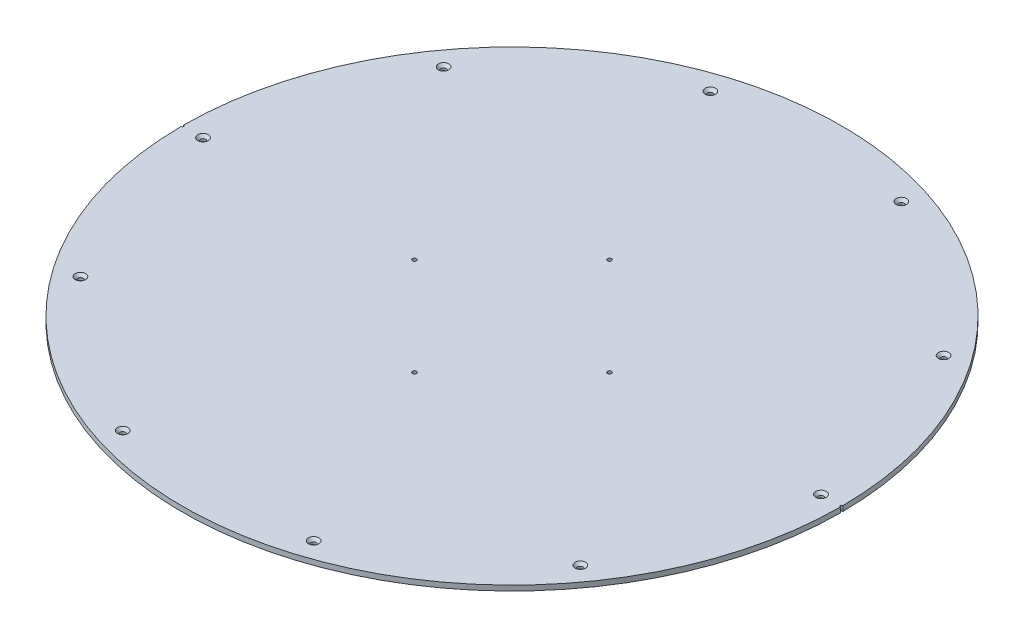
SolidWorks part; units mm, degrees
material "PC High Viscosity"
ref_plane "Front Plane" through (0, 0, 0) normal (0, 0, 1) x (1, 0, 0)
ref_plane "Top Plane" through (0, 0, 0) normal (0, 1, 0) x (1, 0, 0)
ref_plane "Right Plane" through (0, 0, 0) normal (1, 0, 0) x (0, 0, -1)
sketch "Sketch1" plane through (0, 0, 0) normal (0, 1, 0) x (1, 0, 0)
  circle A0 centre (0, 0) radius 406.4
  dimension "D1" = 812.8
extrude "Boss-Extrude1" add sketch "Sketch1" along normal blind 6.35
hole_wizard "7/8 (1.125) Diameter Hole1" positions "Sketch2" profile "Sketch3" hole size "7/8" standard "ANSI Inch"
sketch "Sketch2" plane through (0, 6.35, 0) normal (0, 1, 0) x (1, 0, 0)
  point P0 (0, 0)
sketch "Sketch3" plane through (0, 6.35, 0) normal (1, 0, 0) x (0, 0, 1)
  line L0 (0, 0) -> (0, 6.35)
  line L1 (0, 6.35) -> (14.2875, 6.35)
  line L2 (14.2875, 6.35) -> (14.2875, 0)
  line L5 (14.2875, 0) -> (0, 0)
  line L11 (0, -6.35) -> (0, 107.95) construction
  dimension "Thru Hole Dia." = 28.575
  dimension "Thru Hole Depth" = 6.35
hole_wizard "CSK for 1/4 Flat Head Machine Screw1" positions "Sketch4" profile "Sketch6" countersink size "1/4" standard "ANSI Inch"
sketch "Sketch4" plane through (0, 6.35, 0) normal (0, 1, 0) x (1, 0, 0)
  line L1 (0, 0) -> (-238.5946, -328.3973) construction
  line L2 (0, 0) -> (-386.0541, -125.4366) construction
  line L3 (0, 0) -> (-386.0541, 125.4366) construction
  line L4 (0, 0) -> (-238.5946, 328.3973) construction
  line L5 (0, 0) -> (0, 405.9213) construction
  line L6 (0, 0) -> (238.5946, 328.3973) construction
  line L7 (0, 0) -> (386.0541, 125.4366) construction
  line L8 (0, 0) -> (386.0541, -125.4366) construction
  line L9 (0, 0) -> (0, -406.4) construction
  line L11 (0, 0) -> (238.8759, -328.7845) construction
  circle A0 centre (0, 0) radius 406.4 construction
  circle A1 centre (0, 0) radius 76.2
  circle A2 centre (0, 0) radius 381
  point P86 (71.842, -71.842)
  point P88 (0, -101.6)
  point P90 (-71.842, -71.842)
  point P92 (-101.6, 0)
  point P94 (-71.842, 71.842)
  point P159 (117.7355, 362.3525)
  point P161 (308.2355, 223.9462)
  point P163 (381, 0)
  point P165 (308.2355, -223.9462)
  point P167 (117.7355, -362.3525)
  point P169 (-117.7355, -362.3525)
  point P171 (-308.2355, -223.9462)
  point P173 (-381, 0)
  point P175 (-308.2355, 223.9462)
  point P177 (-117.7355, 362.3525)
  point P183 (0, 76.2)
  point P185 (-76.2, 0)
  point P193 (223.9462, -308.2355)
  point P195 (0, -381)
  point P197 (-223.9462, -308.2355)
  point P199 (-362.3525, -117.7355)
  point P201 (-362.3525, 117.7355)
  point P203 (-223.9462, 308.2355)
  point P206 (223.9462, 308.2355)
  point P208 (362.3525, 117.7355)
  point P210 (362.3525, -117.7355)
  dimension "D2" = 117.7355
  dimension "D4" = 36
  dimension "D6" = 36
  dimension "D3" = 117.7355
  dimension "D5" = 36
  dimension "D7" = 36
  dimension "D8" = 36
  dimension "D9" = 36
  dimension "D10" = 36
  dimension "D11" = 36
  dimension "D12" = 36
  dimension "D13" = 117.7355
  dimension "D14" = 117.7355
  dimension "D15" = 117.7355
  dimension "D16" = 117.7355
  dimension "D17" = 117.7355
  dimension "D18" = 117.7355
  dimension "D19" = 117.7355
  dimension "D20" = 117.7355
sketch "Sketch6" plane through (-117.7355, 6.35, -362.3525) normal (1, 0, 0) x (0, 0, 1)
  line L0 (0, 0) -> (0, 6.35)
  line L1 (0, 6.35) -> (3.3782, 6.35)
  line L2 (3.3782, 6.35) -> (3.3782, 3.5209)
  line L3 (3.3782, 3.5209) -> (6.4389, 0)
  line L5 (6.4389, 0) -> (0, 0)
  line L6 (-3.3782, 3.5209) -> (-6.4389, 0) construction
  line L11 (0, -6.35) -> (0, 107.95) construction
  dimension "Thru Hole Dia." = 6.7564
  dimension "Thru Hole Depth" = 6.35
  dimension "Near C'Sink Dia." = 12.8778
  dimension "Near C'Sink Angle" = 82
hole_wizard "#10 (0.1935) Diameter Hole1" positions "Sketch7" profile "Sketch8" hole size "#10" standard "ANSI Inch" end condition through all
sketch "Sketch7" plane through (0, 6.35, 0) normal (0, 1, 0) x (1, 0, 0)
  line L0 (0, 0) -> (0, 120.2563) construction
  line L2 (0, 0) -> (0, -124.1671) construction
  line L3 (0, 0) -> (120.2563, 0) construction
  line L5 (0, 0) -> (-120.2563, 0) construction
  circle A0 centre (0, 0) radius 120.2563
  point P0 (0, -120.2563)
  point P2 (120.2563, 0)
  point P4 (0, 120.2563)
  point P6 (-120.2563, 0)
  dimension "D1" = 240.5126
  dimension "D2" = 90
sketch "Sketch8" plane through (0, 6.35, 120.2563) normal (1, 0, 0) x (0, 0, 1)
  line L0 (0, 0) -> (0, 6.35)
  line L1 (0, 6.35) -> (2.4574, 6.35)
  line L2 (2.4574, 6.35) -> (2.4574, 0)
  line L5 (2.4574, 0) -> (0, 0)
  line L11 (0, -6.35) -> (0, 107.95) construction
  dimension "Thru Hole Dia." = 4.9149
  dimension "Thru Hole Depth" = 6.35
hole_wizard "1/8 (0.125) Diameter Hole1" positions "Sketch9" profile "Sketch10" hole size "1/8" standard "ANSI Inch" end condition through all
sketch "Sketch9" plane through (0, 6.35, 0) normal (0, 1, 0) x (1, 0, 0)
  circle A0 centre (0, 0) radius 406.4 construction
  point P0 (-406.4, 0)
  point P4 (406.4, 0)
  point P8 (0, 0)
  point P9 (0, 0)
  point P10 (-406.4, 0)
  point P11 (-406.4, 0)
sketch "Sketch10" plane through (-406.4, 6.35, 0) normal (1, 0, 0) x (0, 0, 1)
  line L0 (0, 0) -> (0, 6.35)
  line L1 (0, 6.35) -> (1.5875, 6.35)
  line L2 (1.5875, 6.35) -> (1.5875, 0)
  line L5 (1.5875, 0) -> (0, 0)
  line L11 (0, -6.35) -> (0, 107.95) construction
  dimension "Thru Hole Dia." = 3.175
  dimension "Thru Hole Depth" = 6.35
